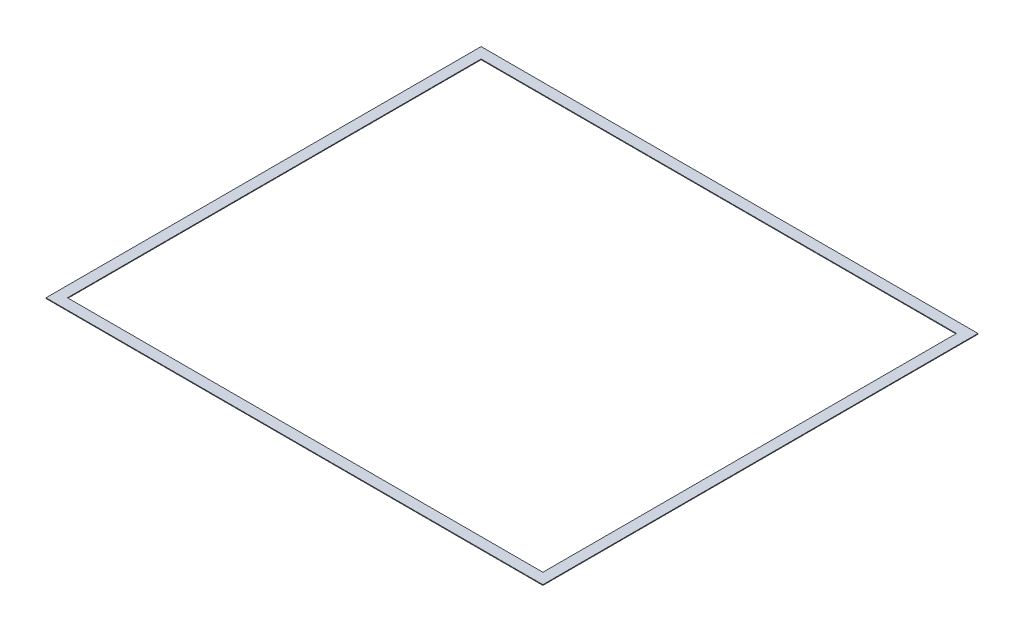
SolidWorks part; units mm, degrees
ref_plane "Front Plane" through (0, 0, 0) normal (0, 0, 1) x (1, 0, 0)
ref_plane "Top Plane" through (0, 0, 0) normal (0, 1, 0) x (1, 0, 0)
ref_plane "Right Plane" through (0, 0, 0) normal (1, 0, 0) x (0, 0, -1)
sketch "Sketch1" plane through (0, 0, 0) normal (0, 1, 0) x (1, 0, 0)
  line L1 (-1174.75, 1028.7) -> (1174.75, 1028.7)
  line L2 (-1174.75, 1028.7) -> (-1174.75, -1028.7)
  line L3 (-1174.75, -1028.7) -> (1174.75, -1028.7)
  line L4 (1174.75, 1028.7) -> (1174.75, -1028.7)
  line L5 (-1174.75, 1028.7) -> (1174.75, -1028.7) construction
  line L6 (-1174.75, -1028.7) -> (1174.75, 1028.7) construction
  line L7 (-1123.95, 977.9) -> (1123.95, 977.9)
  line L8 (-1123.95, 977.9) -> (-1123.95, -977.9)
  line L9 (-1123.95, -977.9) -> (1123.95, -977.9)
  line L10 (1123.95, 977.9) -> (1123.95, -977.9)
  line L11 (-1123.95, 977.9) -> (1123.95, -977.9) construction
  line L12 (-1123.95, -977.9) -> (1123.95, 977.9) construction
  point P0 (0, 0)
  point P6 (0, 0)
  dimension "D1" = 50.8
  dimension "D2" = 50.8
  dimension "D3" = 2298.7
  dimension "D4" = 2057.4
extrude "Boss-Extrude1" add sketch "Sketch1" along normal blind 3.175
